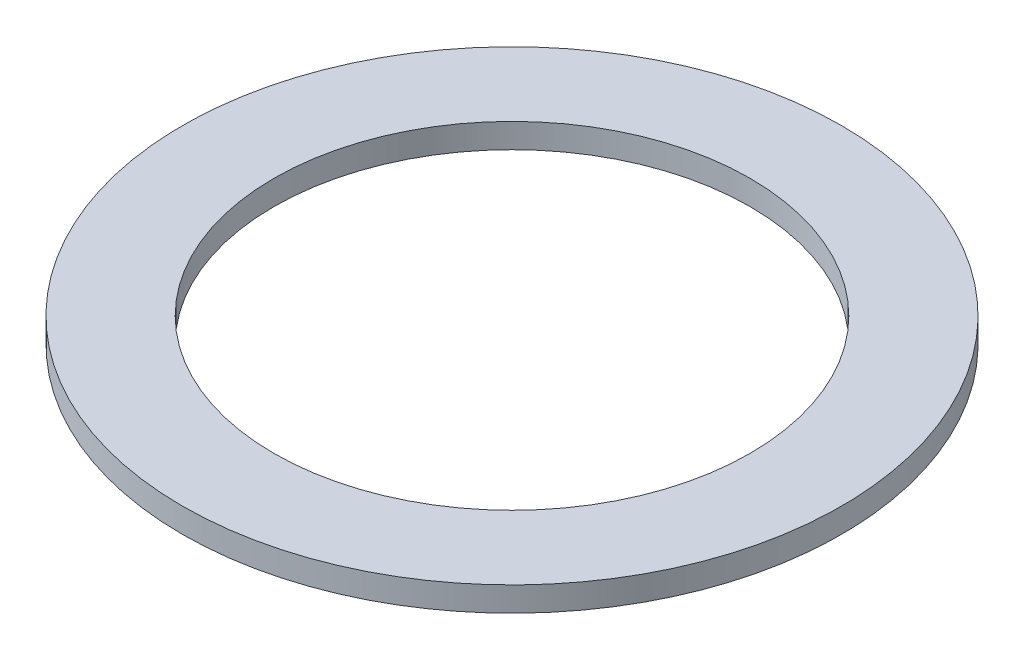
SolidWorks part; units mm, degrees
ref_plane "Front Plane" through (0, 0, 0) normal (0, 0, 1) x (1, 0, 0)
ref_plane "Top Plane" through (0, 0, 0) normal (0, 1, 0) x (1, 0, 0)
ref_plane "Right Plane" through (0, 0, 0) normal (1, 0, 0) x (0, 0, -1)
sketch "Sketch1" plane through (0, 0, 0) normal (0, 0, 1) x (1, 0, 0)
  line L1 (19.4945, 2.0066) -> (26.9748, 2.0066)
  line L2 (19.4945, 2.0066) -> (19.4945, 0)
  line L3 (19.4945, 0) -> (26.9748, 0)
  line L4 (26.9748, 2.0066) -> (26.9748, 0)
  point P4 (0, 0)
  dimension "D1" = 19.4945
  dimension "D2" = 26.9748
  dimension "D3" = 2.0066
ref_axis "central axis" through (0, 0.1952, 0) along (0, 1, 0)
revolve "Revolve1" add sketch "Sketch1" angle 360 about axis through (0, 0.1952, 0) along (0, 1, 0)
